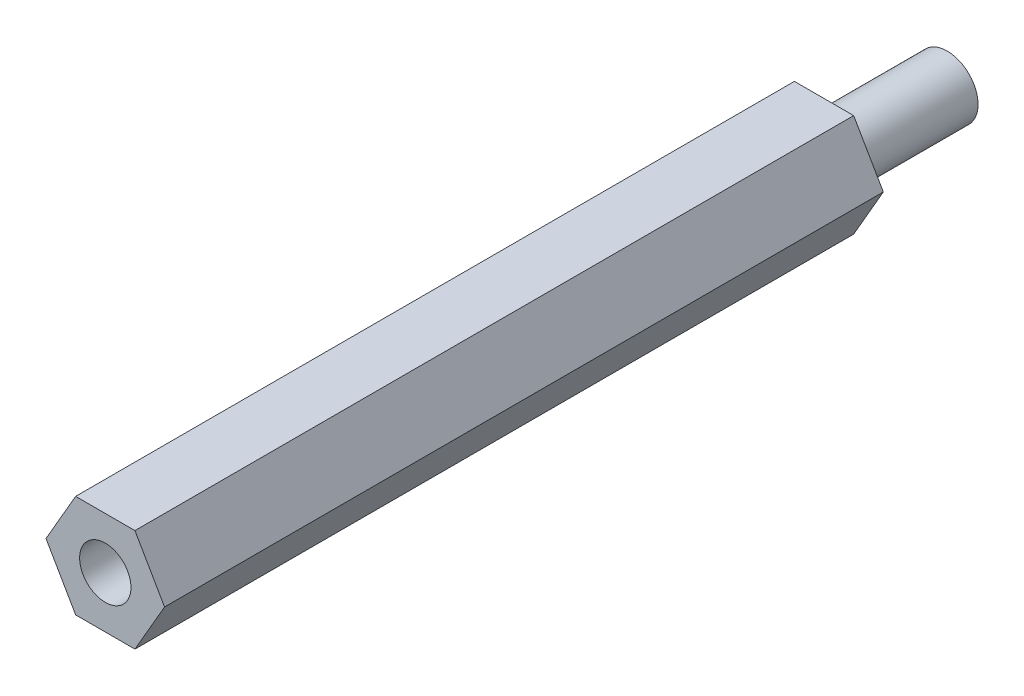
SolidWorks part; units mm, degrees
material "黃銅"
ref_plane "前基準面" through (0, 0, 0) normal (0, 0, 1) x (1, 0, 0)
ref_plane "上基準面" through (0, 0, 0) normal (0, 1, 0) x (1, 0, 0)
ref_plane "右基準面" through (0, 0, 0) normal (1, 0, 0) x (0, 0, -1)
sketch "草圖1" plane through (0, 0, 0) normal (0, 0, 1) x (1, 0, 0)
  line L1 (-1.4434, 2.5) -> (-2.8868, 0)
  line L2 (-2.8868, 0) -> (-1.4434, -2.5)
  line L3 (-1.4434, -2.5) -> (1.4434, -2.5)
  line L4 (1.4434, -2.5) -> (2.8868, 0)
  line L5 (2.8868, 0) -> (1.4434, 2.5)
  line L6 (1.4434, 2.5) -> (-1.4434, 2.5)
  circle A0 centre (0, 0) radius 2.5 construction
  dimension "D1" = 5
extrude "填料-伸長1" add sketch "草圖1" along normal blind 35
sketch "草圖4" plane through (0, 0, 0) normal (0, 0, -1) x (-1, 0, 0)
  circle A0 centre (0, 0) radius 1.5
  dimension "D1" = 3
extrude "填料-伸長2" add sketch "草圖4" along normal blind 6
hole_wizard "M3x0.5 螺紋孔1" positions "草圖2" profile "草圖3" tap size "M3x0.5" standard "Ansi Metric"
sketch "草圖2" plane through (0, 0, 35) normal (0, 0, 1) x (1, 0, 0)
  point P0 (0, 0)
sketch "草圖3" plane through (0, 0, 35) normal (1, 0, 0) x (0, -1, 0)
  line L0 (0, 0) -> (0, 8.2511)
  line L1 (0, 8.2511) -> (1.25, 7.5)
  line L2 (1.25, 7.5) -> (1.25, 0)
  line L5 (1.25, 0) -> (0, 0)
  line L10 (0, 8.2511) -> (-1.25, 7.5) construction
  line L11 (0, -6.35) -> (0, 107.95) construction
  dimension "螺孔鑽直徑" = 2.5
  dimension "螺孔鑽深度" = 7.5
  dimension "導頭角度" = 118
